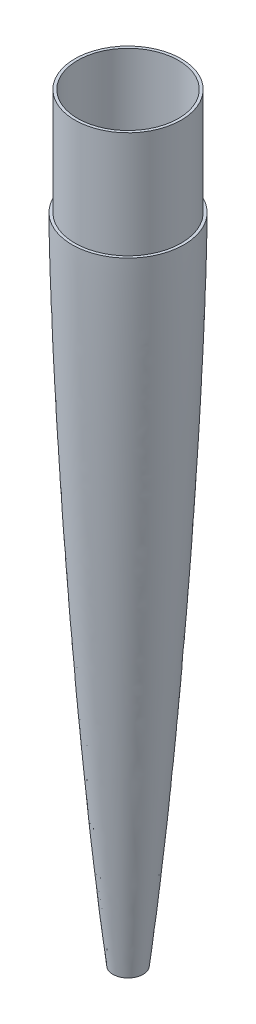
SolidWorks part; units mm, degrees
ref_plane "Front Plane" through (0, 0, 0) normal (0, 0, 1) x (1, 0, 0)
ref_plane "Top Plane" through (0, 0, 0) normal (0, 1, 0) x (1, 0, 0)
ref_plane "Right Plane" through (0, 0, 0) normal (1, 0, 0) x (0, 0, -1)
sketch "Sketch1" plane through (0, 0, 0) normal (0, 0, 1) x (1, 0, 0)
  line L0 (-60, 0) -> (-57.03, 0)
  line L1 (0, -789.4472) -> (0, -579.6585) construction
  line L4 (0, -800) -> (0, -789.4472) construction
  line L5 (-13.5025, -696.7824) -> (-13.1644, -699.67)
  line L7 (-54.06, 0) -> (-54.9769, -95.2674)
  line L9 (-57.03, 0) -> (-57.03, 114.3)
  line L10 (-57.03, 114.3) -> (-54.06, 114.3)
  line L11 (-54.06, 0) -> (-54.06, 114.3)
  line L12 (0, -699.67) -> (-13.1644, -699.67) construction
  line L13 (-13.1644, -699.67) -> (-16.1549, -699.67)
  spline S1 degree 3 poles (-16.1549, -699.67) (-16.0778, -700.3264) (-15.9146, -701.7116) (-15.6637, -703.8251) (-15.4033, -706.0112) (-15.1403, -708.1968) (-14.7877, -711.1115) (-14.431, -714.0256) (-14.0705, -716.94) (-13.7976, -719.1256) (-13.5232, -721.3117) (-13.2464, -723.4974) (-12.967, -725.6834) (-12.6855, -727.8691) (-12.4017, -730.0548) (-12.1149, -732.2404) (-11.8261, -734.4262) (-11.5335, -736.6122) (-11.2396, -738.798) (-10.9412, -740.9839) (-10.641, -743.1697) (-10.3368, -745.3557) (-10.0294, -747.5414) (-9.7189, -749.7271) (-9.404, -751.9128) (-9.0856, -754.0985) (-8.7627, -756.2845) (-8.4361, -758.4703) (-8.1038, -760.6562) (-7.7675, -762.842) (-7.4253, -765.0277) (-7.0775, -767.2135) (-6.7236, -769.3992) (-6.3629, -771.5853) (-5.9952, -773.7711) (-5.6185, -775.9572) (-5.234, -778.143) (-4.8375, -780.3289) (-4.4328, -782.5152) (-4.0092, -784.7007) (-3.5793, -786.8876) (-3.1137, -789.0724) (-2.656, -791.2623) (-2.1075, -793.4442) (-1.6286, -795.6455) (-0.8407, -797.8415) (-0.5824, -799.3519) (0, -800) knots 0.873265 0.873265 0.873265 0.873265 0.875734 0.878475 0.881216 0.883958 0.886699 0.892184 0.894926 0.897669 0.900412 0.903156 0.9059 0.908645 0.911389 0.914134 0.91688 0.919625 0.922373 0.925119 0.927867 0.930615 0.933364 0.936113 0.938862 0.941613 0.944364 0.947117 0.949869 0.952624 0.955378 0.958134 0.960892 0.96365 0.966411 0.969172 0.971937 0.974702 0.977471 0.980243 0.983018 0.985799 0.988585 0.991381 0.994189 0.997025 1 1 1 1 construction
  spline S2 degree 3 poles (-13.1644, -699.67) (-12.9236, -701.718) (-12.2672, -707.2495) (-10.5963, -720.9652) (-8.031, -740.7984) (-5.0833, -761.1793) (-2.3992, -777.4138) (-0.8567, -785.4439) (0, -789.4472) knots 0.8737 0.8737 0.8737 0.8737 0.881411 0.894531 0.925377 0.956223 0.971646 0.987069 0.987069 0.987069 0.987069 construction
  spline S4 degree 3 poles (-60, 0) (-60, -0.8013) (-59.9929, -2.1349) (-59.9805, -4.3959) (-59.9625, -6.5446) (-59.9428, -8.7499) (-59.9191, -10.9255) (-59.8941, -13.1168) (-59.8662, -15.2995) (-59.8366, -17.4868) (-59.8051, -19.6717) (-59.7715, -21.8581) (-59.7369, -24.0435) (-59.7, -26.2297) (-59.662, -28.4153) (-59.6225, -30.6013) (-59.5815, -32.787) (-59.539, -34.9727) (-59.4956, -37.1584) (-59.4503, -39.3441) (-59.4045, -41.5301) (-59.3568, -43.7158) (-59.3086, -45.9018) (-59.2586, -48.0875) (-59.2081, -50.2732) (-59.1558, -52.4589) (-59.1035, -54.6446) (-59.0483, -56.8306) (-58.9943, -59.0163) (-58.9382, -61.2023) (-58.8811, -63.388) (-58.8234, -65.574) (-58.7644, -67.7597) (-58.7047, -69.9454) (-58.6439, -72.1311) (-58.5823, -74.3168) (-58.5197, -76.5028) (-58.4565, -78.6885) (-58.3921, -80.8745) (-58.3271, -83.0602) (-58.2612, -85.246) (-58.1942, -87.4317) (-58.1273, -89.6174) (-58.0586, -91.8033) (-57.9893, -93.9889) (-57.9195, -96.175) (-57.8486, -98.3607) (-57.7772, -100.5467) (-57.7051, -102.7324) (-57.6078, -105.6469) (-57.5088, -108.561) (-57.4086, -111.4755) (-57.3329, -113.6612) (-57.256, -115.8472) (-57.179, -118.0329) (-57.1007, -120.2185) (-57.022, -122.4042) (-56.9429, -124.5899) (-56.8623, -126.7759) (-56.7822, -128.9616) (-56.6997, -131.1476) (-56.6183, -133.3334) (-56.5355, -135.5194) (-56.4521, -137.7051) (-56.368, -139.8907) (-56.2833, -142.0764) (-56.198, -144.2621) (-56.1119, -146.4481) (-56.0255, -148.6338) (-55.9379, -150.8198) (-55.8503, -153.0055) (-55.7613, -155.1912) (-55.6431, -158.1054) (-55.5227, -161.0199) (-55.4016, -163.9343) (-55.3099, -166.1203) (-55.2181, -168.306) (-55.1248, -170.492) (-55.0321, -172.6777) (-54.9376, -174.8634) (-54.8436, -177.0491) (-54.748, -179.2348) (-54.6526, -181.4208) (-54.5565, -183.6065) (-54.4595, -185.7925) (-54.3622, -187.9782) (-54.2643, -190.1639) (-54.1656, -192.3496) (-54.0666, -194.5353) (-53.9668, -196.7213) (-53.8667, -198.907) (-53.7659, -201.093) (-53.6647, -203.2787) (-53.5626, -205.4647) (-53.4602, -207.6504) (-53.3575, -209.8361) (-53.2538, -212.0218) (-53.1499, -214.2075) (-53.0452, -216.3935) (-52.94, -218.5792) (-52.8343, -220.7652) (-52.728, -222.9509) (-52.6216, -225.1366) (-52.5138, -227.3223) (-52.4067, -229.508) (-52.2972, -231.694) (-52.1899, -233.8797) (-52.0791, -236.0657) (-51.9699, -238.2514) (-51.859, -240.4374) (-51.7483, -242.6231) (-51.6367, -244.8088) (-51.5246, -246.9945) (-51.4123, -249.1802) (-51.2989, -251.3662) (-51.1858, -253.5519) (-51.0711, -255.7379) (-50.9569, -257.9236) (-50.8414, -260.1093) (-50.7262, -262.295) (-50.6098, -264.4807) (-50.4931, -266.6667) (-50.3761, -268.8524) (-50.2582, -271.0384) (-50.1402, -273.2241) (-50.0213, -275.41) (-49.9023, -277.5957) (-49.7825, -279.7813) (-49.6622, -281.9672) (-49.5416, -284.1528) (-49.4202, -286.3389) (-49.2988, -288.5246) (-49.1758, -290.7106) (-49.0546, -292.8963) (-48.9296, -295.0819) (-48.807, -297.2677) (-48.6822, -299.4533) (-48.5576, -301.6394) (-48.4324, -303.8251) (-48.3066, -306.0111) (-48.1383, -308.9256) (-47.9688, -311.84) (-47.7987, -314.7542) (-47.6703, -316.9398) (-47.5417, -319.1255) (-47.4122, -321.3116) (-47.2825, -323.4973) (-47.1525, -325.6833) (-47.0216, -327.869) (-46.8905, -330.0547) (-46.7584, -332.2403) (-46.6266, -334.426) (-46.4937, -336.612) (-46.3605, -338.7977) (-46.2267, -340.9838) (-46.0927, -343.1695) (-45.9577, -345.3554) (-45.8228, -347.5411) (-45.6865, -349.7267) (-45.5513, -351.9126) (-45.414, -354.0982) (-45.2766, -356.2842) (-45.1391, -358.4699) (-45.0008, -360.656) (-44.862, -362.8417) (-44.7229, -365.0274) (-44.583, -367.213) (-44.4431, -369.3987) (-44.3019, -371.5847) (-44.1609, -373.7704) (-44.0192, -375.9564) (-43.8768, -378.1421) (-43.7342, -380.3279) (-43.5909, -382.5136) (-43.4471, -384.6993) (-43.3028, -386.8852) (-43.158, -389.0709) (-43.0129, -391.2569) (-42.8669, -393.4426) (-42.7207, -395.6286) (-42.5738, -397.8143) (-42.4265, -400) (-42.2786, -402.1857) (-42.1303, -404.3714) (-41.9816, -406.5574) (-41.8317, -408.7431) (-41.6828, -410.9292) (-41.5315, -413.1148) (-41.3304, -416.0293) (-41.1281, -418.9434) (-40.9247, -421.8579) (-40.7717, -424.0436) (-40.6181, -426.2296) (-40.464, -428.4153) (-40.3092, -430.6013) (-40.1543, -432.787) (-39.9986, -434.9727) (-39.8422, -437.1584) (-39.6858, -439.3441) (-39.5281, -441.5301) (-39.3707, -443.7158) (-39.2119, -445.9018) (-39.0534, -448.0875) (-38.8936, -450.2733) (-38.7337, -452.459) (-38.5732, -454.6447) (-38.4121, -456.8306) (-38.2506, -459.0163) (-38.0881, -461.2023) (-37.9257, -463.388) (-37.762, -465.574) (-37.598, -467.7597) (-37.4343, -469.9454) (-37.2688, -472.131) (-37.1036, -474.3168) (-36.9373, -476.5028) (-36.7707, -478.6885) (-36.6033, -480.8745) (-36.4356, -483.0602) (-36.2672, -485.2459) (-36.098, -487.4316) (-35.9287, -489.6173) (-35.7583, -491.8033) (-35.5877, -493.989) (-35.4164, -496.175) (-35.2444, -498.3607) (-35.072, -500.5467) (-34.8989, -502.7324) (-34.6672, -505.6469) (-34.4346, -508.5611) (-34.2003, -511.4755) (-34.0243, -513.6612) (-33.8474, -515.8471) (-33.6708, -518.0329) (-33.4917, -520.2187) (-33.3136, -522.4044) (-33.1342, -524.5901) (-32.9542, -526.7759) (-32.774, -528.9617) (-32.5924, -531.1477) (-32.4109, -533.3334) (-32.2282, -535.5194) (-32.0451, -537.7051) (-31.8612, -539.8907) (-31.6767, -542.0764) (-31.492, -544.2622) (-31.3059, -546.4482) (-31.1193, -548.6338) (-30.9323, -550.8199) (-30.7445, -553.0056) (-30.556, -555.1913) (-30.3665, -557.3769) (-30.1772, -559.5627) (-29.9857, -561.7486) (-29.7949, -563.9344) (-29.6027, -566.1204) (-29.4099, -568.3061) (-29.2165, -570.4921) (-29.0221, -572.6778) (-28.8273, -574.8635) (-28.6313, -577.0491) (-28.4352, -579.2348) (-28.2375, -581.4208) (-28.0398, -583.6065) (-27.8408, -585.7925) (-27.6414, -587.9782) (-27.4411, -590.1639) (-27.2398, -592.3496) (-27.038, -594.5353) (-26.8348, -596.7213) (-26.6319, -598.9071) (-26.4266, -601.093) (-26.2222, -603.2788) (-26.0156, -605.4647) (-25.8089, -607.6504) (-25.601, -609.8361) (-25.3924, -612.0218) (-25.1829, -614.2075) (-24.9723, -616.3935) (-24.7612, -618.5792) (-24.5487, -620.7652) (-24.3356, -622.9509) (-24.1217, -625.1367) (-23.9063, -627.3223) (-23.6908, -629.508) (-23.4731, -631.694) (-23.2563, -633.8798) (-23.0363, -636.0657) (-22.8168, -638.2515) (-22.5956, -640.4375) (-22.3738, -642.6232) (-22.1506, -644.8088) (-21.9265, -646.9945) (-21.7017, -649.1802) (-21.4749, -651.3662) (-21.248, -653.5519) (-21.019, -655.7379) (-20.7898, -657.9237) (-20.4816, -660.8382) (-20.1719, -663.7524) (-19.8593, -666.6668) (-19.6238, -668.8524) (-19.3867, -671.0384) (-19.1486, -673.2242) (-18.9089, -675.4102) (-18.6684, -677.5959) (-18.426, -679.7815) (-18.1825, -681.9672) (-17.9376, -684.1529) (-17.6911, -686.3389) (-17.3605, -689.2535) (-17.0271, -692.168) (-16.6903, -695.082) (-16.4364, -697.2677) (-16.2574, -698.797) (-16.1634, -699.5979) (-16.1549, -699.67) knots 0 0 0 0 0.002721 0.005444 0.008165 0.010888 0.013609 0.016332 0.019054 0.021775 0.024498 0.02722 0.029942 0.032664 0.035387 0.038109 0.040832 0.043554 0.046275 0.048999 0.051721 0.054444 0.057166 0.059889 0.062611 0.065333 0.068056 0.070778 0.073502 0.076224 0.078948 0.08167 0.084393 0.087116 0.089838 0.092562 0.095284 0.098008 0.10073 0.103454 0.106176 0.108899 0.111623 0.114345 0.117069 0.119792 0.122516 0.125239 0.127963 0.130686 0.136133 0.138855 0.14158 0.144303 0.147027 0.14975 0.152473 0.155197 0.15792 0.160645 0.163368 0.166092 0.168816 0.17154 0.174263 0.176987 0.179711 0.182435 0.185159 0.187883 0.190608 0.193331 0.196055 0.201503 0.204228 0.206952 0.209677 0.212401 0.215126 0.217849 0.220573 0.223298 0.226022 0.228747 0.231471 0.234197 0.236921 0.239645 0.24237 0.245094 0.247819 0.250544 0.253269 0.255993 0.258719 0.261443 0.264168 0.266893 0.269618 0.272343 0.275068 0.277794 0.280518 0.283243 0.285968 0.288693 0.291419 0.294144 0.29687 0.299594 0.30232 0.305045 0.30777 0.310496 0.313221 0.315947 0.318672 0.321399 0.324124 0.326849 0.329575 0.332301 0.335027 0.337752 0.340479 0.343204 0.34593 0.348656 0.351381 0.354108 0.356834 0.35956 0.362286 0.365013 0.367738 0.370464 0.373191 0.375917 0.378644 0.381369 0.384096 0.389549 0.392275 0.395001 0.397729 0.400455 0.403182 0.405908 0.408636 0.411362 0.414088 0.416815 0.419542 0.422269 0.424996 0.427723 0.43045 0.433177 0.435904 0.438631 0.441359 0.444085 0.446813 0.44954 0.452268 0.454995 0.457722 0.46045 0.463177 0.465905 0.468632 0.47136 0.474087 0.476815 0.479543 0.48227 0.484999 0.487726 0.490454 0.493182 0.495911 0.498638 0.501366 0.504094 0.506822 0.509551 0.512278 0.515007 0.517735 0.523192 0.52592 0.528649 0.531377 0.534107 0.536835 0.539564 0.542292 0.54502 0.54775 0.550478 0.553208 0.555936 0.558666 0.561395 0.564124 0.566853 0.569582 0.572312 0.575041 0.577771 0.580499 0.58323 0.585959 0.588688 0.591418 0.594147 0.596878 0.599607 0.602337 0.605067 0.607796 0.610527 0.613256 0.615987 0.618717 0.621448 0.624178 0.626909 0.629639 0.6351 0.63783 0.640561 0.643291 0.646023 0.648753 0.651484 0.654215 0.656946 0.659677 0.662408 0.66514 0.667871 0.670603 0.673334 0.676065 0.678797 0.681528 0.684261 0.686992 0.689724 0.692456 0.695187 0.69792 0.700652 0.703385 0.706116 0.708849 0.711581 0.714315 0.717047 0.719779 0.722512 0.725245 0.727979 0.730711 0.733445 0.736178 0.73891 0.741645 0.744378 0.747112 0.749845 0.75258 0.755313 0.758048 0.760781 0.763515 0.76625 0.768984 0.771719 0.774453 0.777189 0.779923 0.782657 0.785393 0.788128 0.790864 0.793599 0.796335 0.79907 0.801807 0.804542 0.807278 0.810015 0.81275 0.815488 0.818224 0.820961 0.823698 0.829172 0.831909 0.834648 0.837385 0.840123 0.842861 0.8456 0.848338 0.851076 0.853816 0.856554 0.859294 0.864774 0.867513 0.870253 0.872994 0.873265 0.873265 0.873265 0.873265
  spline S6 degree 3 poles (-54.9769, -95.2674) (-54.9109, -97.3296) (-54.3349, -115.0574) (-53.078, -149.2812) (-50.276, -214.4221) (-46.0241, -296.8587) (-40.9297, -379.2464) (-36.3367, -445.1211) (-32.618, -494.507) (-28.6013, -543.8673) (-24.2469, -593.1958) (-19.6283, -641.0417) (-16.0637, -674.4733) (-13.9928, -692.5625) (-13.6291, -695.6967) (-13.5025, -696.7824) knots 0.11878 0.11878 0.11878 0.11878 0.126492 0.185075 0.246767 0.370151 0.493535 0.555226 0.616918 0.67861 0.740302 0.801994 0.858277 0.865988 0.870076 0.870076 0.870076 0.870076
  point P3 (-13.6462, -695.5482)
  point P12 (0, -699.67)
  dimension "D1" = 114.3
  dimension "D3" = 2.97
  dimension "D4" = 100.33
revolve "Revolve2" add sketch "Sketch1" angle 360 about L1
